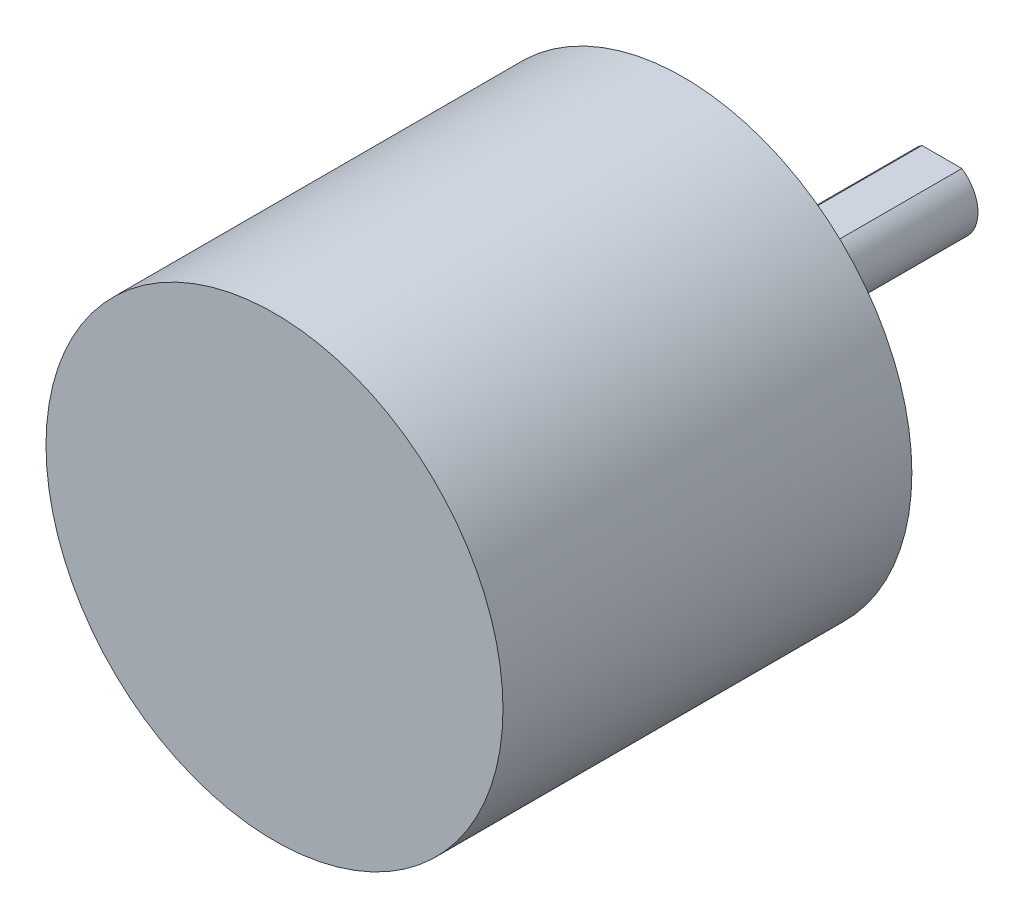
SolidWorks part; units mm, degrees
ref_plane "前视基准面" through (0, 0, 0) normal (0, 0, 1) x (1, 0, 0)
ref_plane "上视基准面" through (0, 0, 0) normal (0, 1, 0) x (1, 0, 0)
ref_plane "右视基准面" through (0, 0, 0) normal (1, 0, 0) x (0, 0, -1)
sketch "草图1" plane through (0, 0, 0) normal (0, 0, 1) x (1, 0, 0)
  circle A0 centre (0, 0) radius 19
extrude "凸台-拉伸1" add sketch "草图1" along normal blind 34
sketch "草图2" plane through (0, 0, 0) normal (0, 0, -1) x (-1, 0, 0)
  circle A0 centre (0, 0) radius 10
extrude "凸台-拉伸2" add sketch "草图2" along normal blind 5
sketch "草图3" plane through (0, 0, -5) normal (0, 0, -1) x (-1, 0, 0)
  circle A0 centre (0, 0) radius 4
extrude "凸台-拉伸3" add sketch "草图3" along normal blind 1
sketch "草图4" plane through (0, 0, -6) normal (0, 0, -1) x (-1, 0, 0)
  circle A0 centre (0, 0) radius 3
extrude "凸台-拉伸4" add sketch "草图4" along normal blind 15.5
sketch "草图5" plane through (0, 0, -21.5) normal (0, 0, -1) x (-1, 0, 0)
  line L0 (0, 3) -> (0, 2.5)
  line L2 (-1.6583, 3.5) -> (1.6583, 3.5)
  line L3 (-1.6583, 3.5) -> (-1.6583, 2.5)
  line L4 (-1.6583, 2.5) -> (1.6583, 2.5)
  line L5 (1.6583, 3.5) -> (1.6583, 2.5)
  line L6 (-1.6583, 3.5) -> (1.6583, 2.5) construction
  line L7 (-1.6583, 2.5) -> (1.6583, 3.5) construction
  circle A0 centre (0, 0) radius 3 construction
  circle M2 centre (0, 0) radius 3
extrude "切除-拉伸2" cut sketch "草图5" against normal blind 12 contours L4 L0 M2 | L0 L4 M2
sketch "草图7" plane through (0, 0, 0) normal (0, 0, -1) x (-1, 0, 0)
  line L0 (0, 15) -> (0, 0) construction
  line L1 (0, 0) -> (-12.9904, -7.5) construction
  line L2 (0, 0) -> (12.9904, -7.5) construction
  circle A0 centre (0, 0) radius 15 construction
  circle A1 centre (0, 15) radius 1.5
  circle A2 centre (-12.9904, -7.5) radius 1.5
  circle A3 centre (12.9904, -7.5) radius 1.5
extrude "切除-拉伸3" cut sketch "草图7" against normal blind 6
